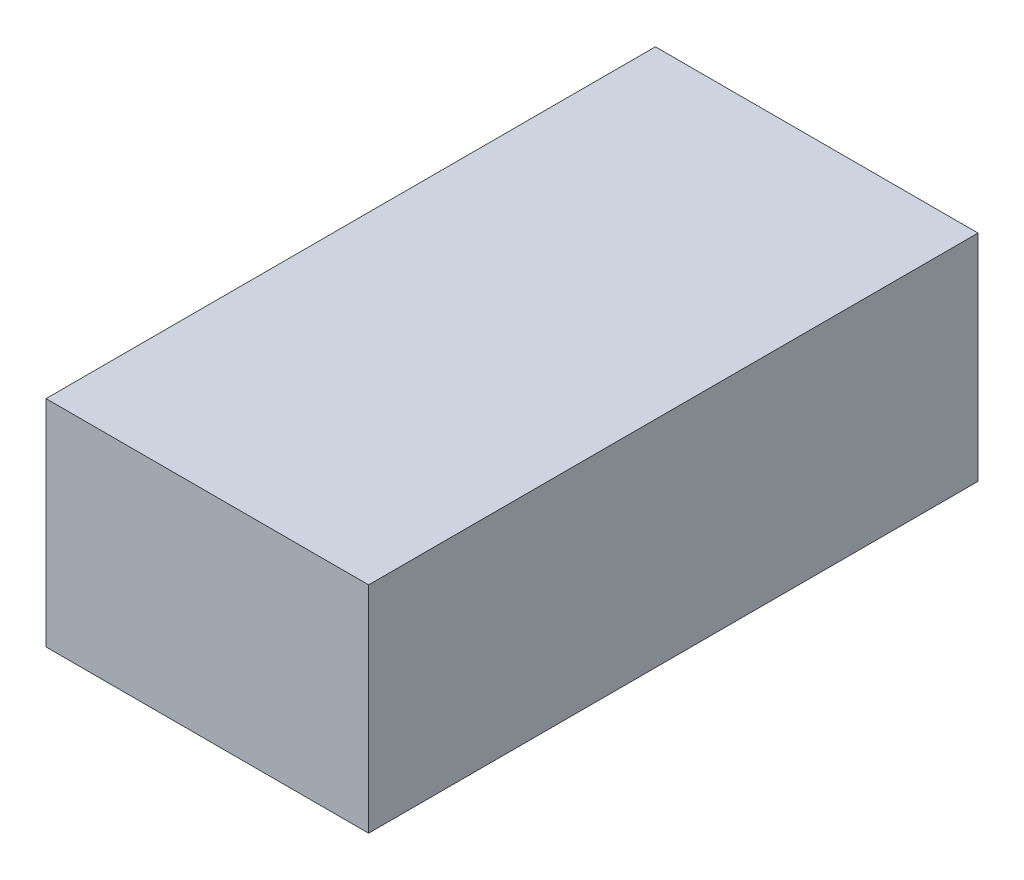
SolidWorks part; units mm, degrees
ref_plane "Front Plane" through (0, 0, 0) normal (0, 0, 1) x (1, 0, 0)
ref_plane "Top Plane" through (0, 0, 0) normal (0, 1, 0) x (1, 0, 0)
ref_plane "Right Plane" through (0, 0, 0) normal (1, 0, 0) x (0, 0, -1)
sketch "Sketch1" plane through (0, 0, 0) normal (0, 1, 0) x (1, 0, 0)
  line L1 (22.5, -42.5) -> (-22.5, -42.5)
  line L2 (22.5, -42.5) -> (22.5, 42.5)
  line L3 (22.5, 42.5) -> (-22.5, 42.5)
  line L4 (-22.5, -42.5) -> (-22.5, 42.5)
  line L5 (22.5, -42.5) -> (-22.5, 42.5) construction
  line L6 (22.5, 42.5) -> (-22.5, -42.5) construction
  point P0 (0, 0)
  dimension "D1" = 85
  dimension "D2" = 45
extrude "Boss-Extrude1" add sketch "Sketch1" along normal blind 30
